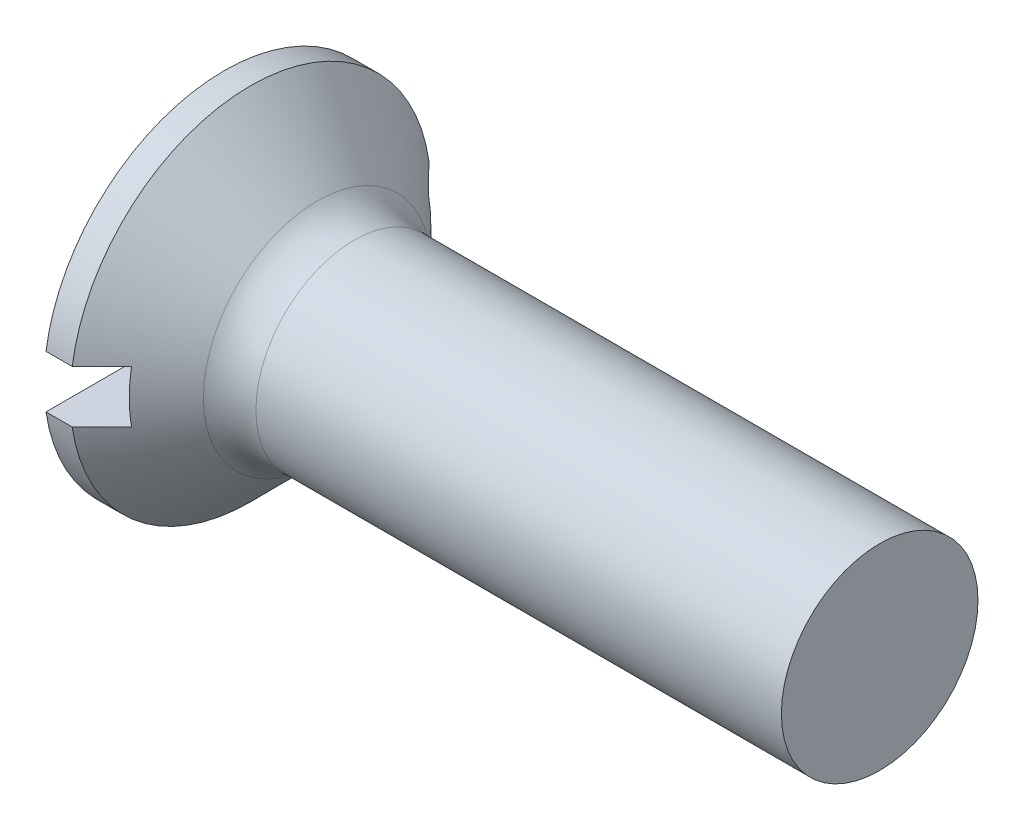
SolidWorks part; units mm, degrees
revolve "Base-Revolve" add sketch "BodySke" angle 360 about L5
sketch "BodySke" plane through (0, 0, 0) normal (0, 0, 1) x (1, 0, 0)
  line L0 (0, 0) -> (0, 2.75)
  line L1 (0, 2.75) -> (0.4, 2.75)
  line L2 (1.65, 1.5) -> (10, 1.5)
  line L3 (10, 1.5) -> (10, 0)
  line L4 (10, 0) -> (0, 0)
  line L5 (-6.35, 0) -> (82.55, 0) construction
  line L6 (1.65, -1.5) -> (10, -1.5) construction
  line L7 (0.4, -2.75) -> (1.65, -1.5) construction
  line L8 (0.4, 2.75) -> (1.65, 1.5)
  line L9 (0, -2.75) -> (0.4, -2.75) construction
  line L10 (2.15, 3.0875) -> (2.15, -6.4375) construction
  line L11 (0, 6.35) -> (0, -3.175) construction
  dimension "Diameter" = 3
  dimension "Length" = 10
  dimension "Head_ht" = 1.65
  dimension "Head_dia" = 5.5
  dimension "Head_ang" = 90
  dimension "D6" = 0.4
  dimension "Advance" = 0.5
  dimension "Thread_nom" = 10
cosmetic thread "ThreadCosmetic" parameters "Thread_length"=7.85, "Thread_minor"=2.439
extrude "Slot" cut sketch "Sketch2" against normal blind 0.85
sketch "Sketch2" plane through (0, 0, 0) normal (-1, 0, 0) x (0, 0, 1)
  line L0 (-2.75, -0.4) -> (2.75, -0.4)
  line L1 (-2.75, -0.4) -> (-2.75, 0.4)
  line L2 (2.75, 0.4) -> (-2.75, 0.4)
  line L3 (2.75, 0.4) -> (2.75, -0.4)
  dimension "Slot_width" = 0.8
  dimension "D1" = 0.4
  dimension "D2" = 5.5
  dimension "D3" = 2.75
ref_plane "Plane1" through (0, 0, 0) normal (0, 0, 1) x (1, 0, 0)
ref_plane "Plane2" through (0, 0, 0) normal (0, 1, 0) x (1, 0, 0)
ref_plane "Plane3" through (0, 0, 0) normal (1, 0, 0) x (0, 0, -1)
fillet "Fillet1" radius 0.8 1 edges at (1.65, 0, 1.5)
sketch "ThdSchSke" plane through (0, 0, 0) normal (0, 0, 1) x (1, 0, 0)
  line L0 (2.15, -1.2195) -> (1.9536, -1.5)
  line L1 (2.15, -1.2195) -> (2.3464, -1.5)
  line L2 (2.3464, -1.5) -> (2.3464, -1.875)
  line L3 (-3.175, 0) -> (5.1513, 0) construction
  line L5 (2.3464, -1.875) -> (1.9536, -1.875)
  line L6 (1.9536, -1.875) -> (1.9536, -1.5)
  line L7 (0, 2.75) -> (0, 0.4) construction
  dimension "Diameter" = 3
  dimension "Thread_minor" = 2.439
  dimension "Start" = 2.15
revolve "ThreadSchematic" [suppressed] cut sketch "ThdSchSke" angle 360 about L3
pattern_linear "ThdSchPat" [suppressed]
equation "\"D1@Sketch2\" = \"Slot_width@Sketch2\" / 2"
equation "\"D2@Sketch2\" = \"Head_dia@BodySke\""
equation "\"D3@Sketch2\" = \"D2@Sketch2\" / 2"
equation "\"Thread_length@ThreadCosmetic\" = ((sgn( (\"Length@BodySke\" - \"Advance@BodySke\" * 1.0 - \"Head_ht@BodySke\" ) - \"Thread_nom@BodySke\" )-1)*( (\"Length@BodySke\" - \"Advance@BodySke\" * 1.0 - \"Head_ht@BodySke\" ) - \"Thread_nom@BodySke\" ))/-2+ \"Thread_nom@BodySke\""
equation "\"Thread_minor@ThdSchSke\" = \"Thread_minor@ThreadCosmetic\""
equation "\"Diameter@ThdSchSke\" = \"Diameter@BodySke\""
equation "\"Overcut@ThdSchSke\" = \"Diameter@BodySke\" * 1.25"
equation "\"Start@ThdSchSke\" = 0.000001 + \"Length@BodySke\" - \"Thread_length@ThreadCosmetic\"  '---Countersunk---"
equation "\"Num_threads@ThdSchPat\" = int( \"Thread_length@ThreadCosmetic\" / \"Advance@BodySke\" + 0.999 )  + 1"
equation "\"Advance@ThdSchPat\" = \"Thread_length@ThreadCosmetic\" /  (\"Num_threads@ThdSchPat\" - 1) 'relax it"
